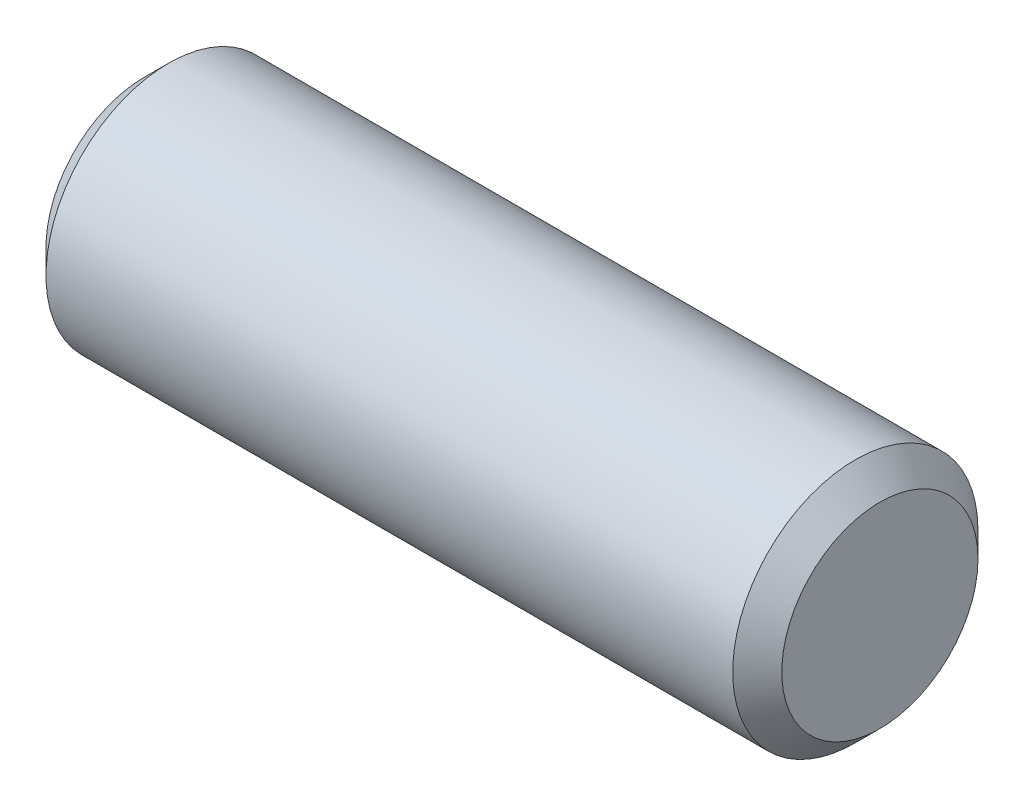
SolidWorks part; units mm, degrees
ref_plane "Front" through (0, 0, 0) normal (0, 0, 1) x (1, 0, 0)
ref_plane "Top" through (0, 0, 0) normal (0, 1, 0) x (1, 0, 0)
ref_plane "Right" through (0, 0, 0) normal (1, 0, 0) x (0, 0, -1)
sketch "Sketch1" plane through (0, 0, 0) normal (0, 0, 1) x (1, 0, 0)
  line L0 (-4.7625, 0) -> (4.7625, 0) construction
  line L1 (4.7625, 1.5875) -> (4.7625, -1.5875) construction
  line L2 (-4.7625, 1.5875) -> (-4.7625, -1.5875) construction
  dimension "Length" = 9.525
  dimension "Diameter" = 3.175
sketch "Sketch2" plane through (0, 0, 0) normal (1, 0, 0) x (0, 0, -1)
  circle A0 centre (0, 0) radius 1.5875
extrude "Extrude1" add sketch "Sketch2" against normal up to vertex (4.7625 mm away) and the other way up to vertex (4.7625 mm away) up to point (-4.7625, 1.5875, 0) other way up to point (4.7625, 1.5875, 0)
chamfer "Chamfer1" distance 0.3175 angle 45 2 edges at (4.7625, 0, -1.5875) (-4.7625, 0, -1.5875)
equation "\"D1@Chamfer1\" = \"Diameter@Sketch1\"*.1"
